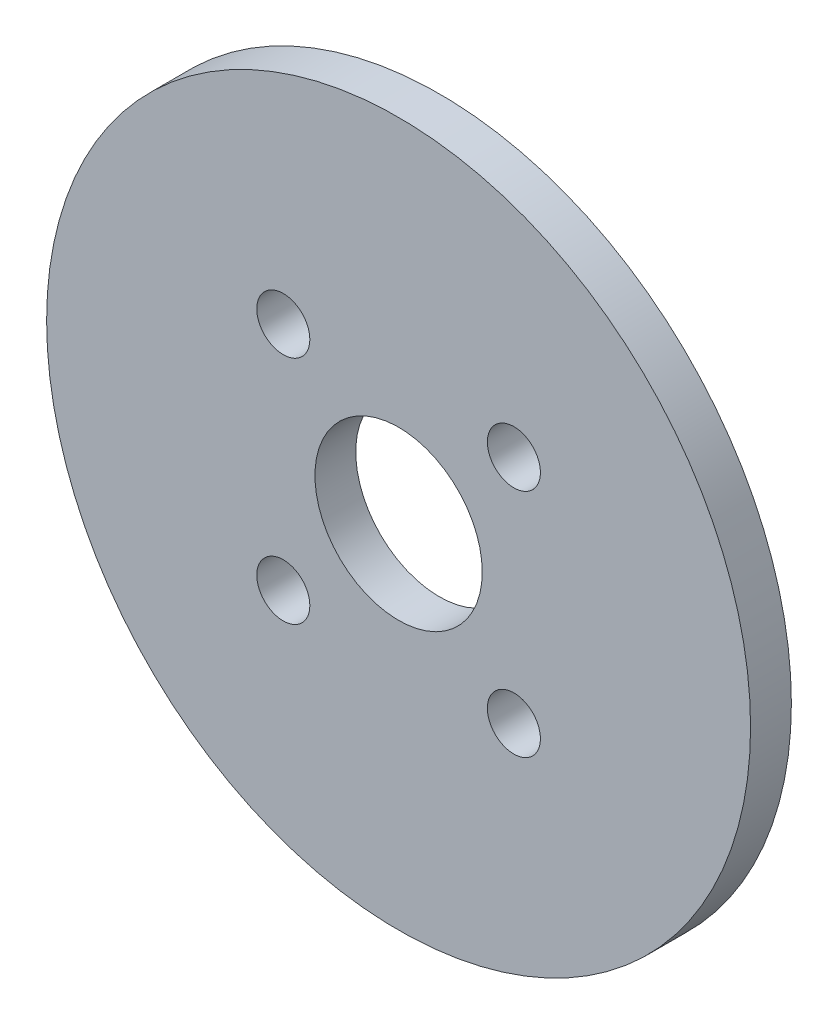
SolidWorks part; units mm, degrees
ref_plane "前视基准面" through (0, 0, 0) normal (0, 0, 1) x (1, 0, 0)
ref_plane "上视基准面" through (0, 0, 0) normal (0, 1, 0) x (1, 0, 0)
ref_plane "右视基准面" through (0, 0, 0) normal (1, 0, 0) x (0, 0, -1)
sketch "草图1" plane through (0, 0, 0) normal (0, 0, 1) x (1, 0, 0)
  line L5 (-5.65, -5.65) -> (5.65, 5.65) construction
  line L6 (-5.65, 5.65) -> (5.65, -5.65) construction
  circle A0 centre (0, 0) radius 17.25
  circle A1 centre (5.65, 5.65) radius 1.3
  circle A2 centre (5.65, -5.65) radius 1.3
  circle A3 centre (-5.65, 5.65) radius 1.3
  circle A4 centre (-5.65, -5.65) radius 1.3
  circle A5 centre (0, 0) radius 4.1
  dimension "D1" = 34.5
  dimension "D3" = 2.6
  dimension "D4" = 2.6
  dimension "D5" = 2.6
  dimension "D6" = 2.6
  dimension "D7" = 8.2
  dimension "D2" = 11.3
extrude "凸台-拉伸1" add sketch "草图1" along normal blind 2
